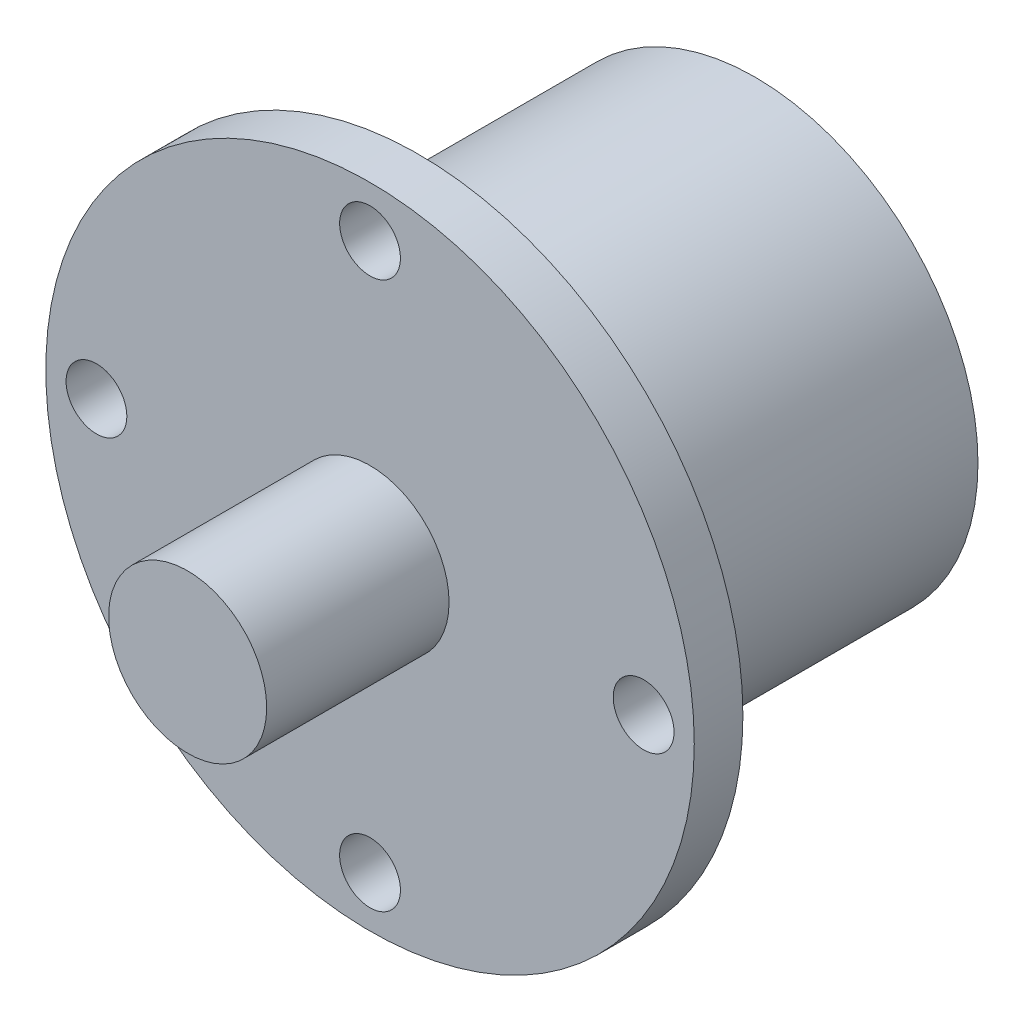
SolidWorks part; units mm, degrees
ref_plane "Спереди" through (0, 0, 0) normal (0, 0, 1) x (1, 0, 0)
ref_plane "Сверху" through (0, 0, 0) normal (0, 1, 0) x (1, 0, 0)
ref_plane "Справа" through (0, 0, 0) normal (1, 0, 0) x (0, 0, -1)
sketch "Эскиз1" plane through (0, 0, 0) normal (0, 0, 1) x (1, 0, 0)
  line L0 (0, 0) -> (0, -50000) construction
  line L1 (0, 0) -> (-50000, 0) construction
  circle A0 centre (0, 0) radius 16
  circle A1 centre (0, 0) radius 13.5 construction
  circle A2 centre (-13.5, 0) radius 1.5
  circle A3 centre (0, 13.5) radius 1.5
  circle A4 centre (13.5, 0) radius 1.5
  circle A5 centre (0, -13.5) radius 1.5
  point P19 (0, 0)
  dimension "D1" = 32
  dimension "D2" = 27
  dimension "D3" = 3
  dimension "D4" = 4
extrude "Бобышка-Вытянуть1" add sketch "Эскиз1" along normal blind 2.4
sketch "Эскиз2" plane through (0, 0, 2.4) normal (0, 0, 1) x (1, 0, 0)
  circle A0 centre (0, 0) radius 3.9
  dimension "D1" = 7.8
extrude "Бобышка-Вытянуть2" add sketch "Эскиз2" along normal blind 9
sketch "Эскиз3" plane through (0, 0, 0) normal (0, 0, -1) x (-1, 0, 0)
  circle A0 centre (0, 0) radius 11
  dimension "D1" = 22
extrude "Бобышка-Вытянуть3" add sketch "Эскиз3" along normal blind 16.6
